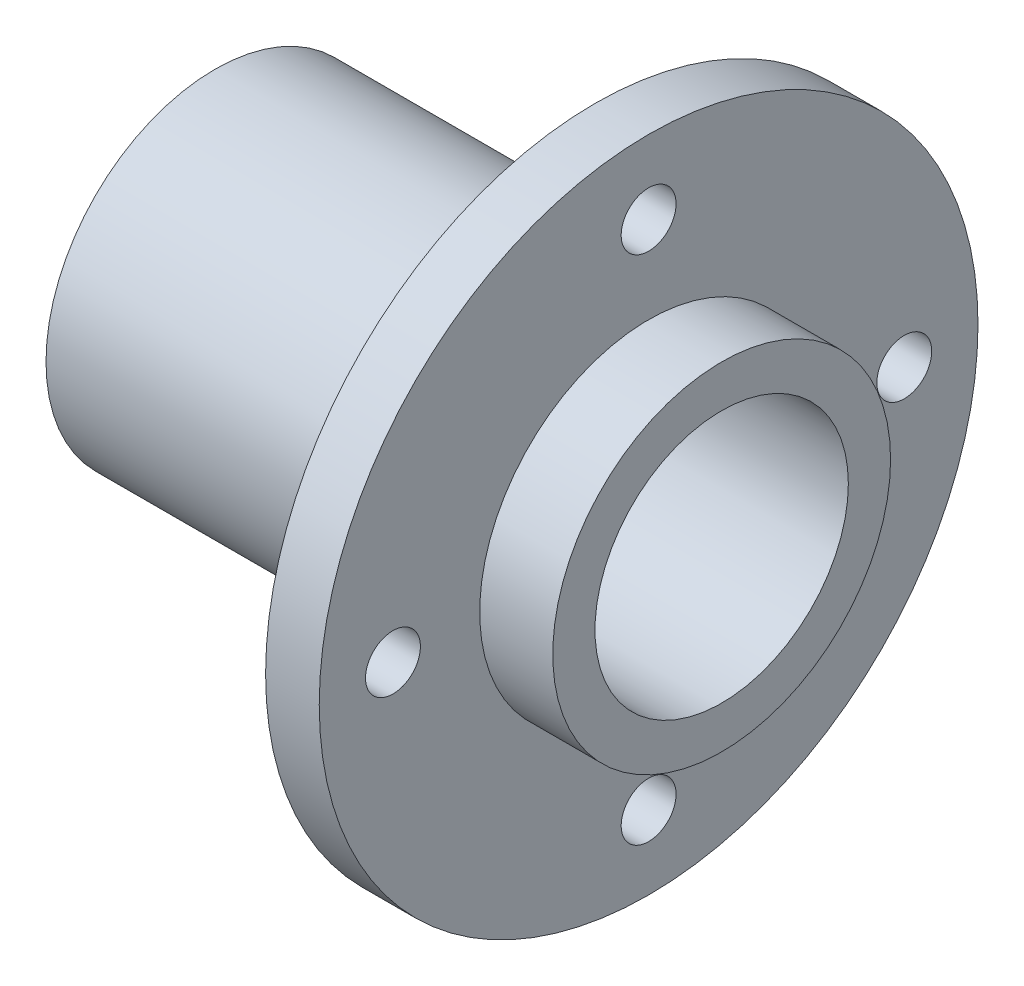
SolidWorks part; units mm, degrees
ref_plane "Front Plane" through (0, 0, 0) normal (0, 0, 1) x (1, 0, 0)
ref_plane "Top Plane" through (0, 0, 0) normal (0, 1, 0) x (1, 0, 0)
ref_plane "Right Plane" through (0, 0, 0) normal (1, 0, 0) x (0, 0, -1)
sketch "Sketch1" plane through (0, 0, 0) normal (1, 0, 0) x (0, 0, -1)
  circle A0 centre (0, 0) radius 39
  dimension "D1" = 78
extrude "Boss-Extrude1" add sketch "Sketch1" along normal blind 6.35
sketch "Sketch2" plane through (6.35, 0, 0) normal (1, 0, 0) x (0, 0, -1)
  circle A0 centre (0, 0) radius 15
  dimension "D1" = 30
extrude "Cut-Extrude1" cut sketch "Sketch2" against normal blind 6.35
sketch "Sketch3" plane through (6.35, 0, 0) normal (1, 0, 0) x (0, 0, -1)
  circle A0 centre (0, 0) radius 20
  circle A1 centre (0, 0) radius 15
  dimension "D1" = 30
  dimension "D2" = 40
extrude "Boss-Extrude2" add sketch "Sketch3" along normal blind 8.65
sketch "Sketch4" plane through (0, 0, 0) normal (-1, 0, 0) x (0, 0, 1)
  circle A0 centre (0, 0) radius 20
  circle A1 centre (0, 0) radius 15
  dimension "D1" = 40
  dimension "D2" = 30
extrude "Boss-Extrude3" add sketch "Sketch4" along normal blind 45
sketch "Sketch5" plane through (0, 0, 0) normal (-1, 0, 0) x (0, 0, 1)
  circle A0 centre (0, 30.27) radius 3.25
  circle A1 centre (-30.27, 0) radius 3.25
  circle A2 centre (30.27, 0) radius 3.25
  circle A3 centre (0, -30.27) radius 3.25
  point P9 (0, 0)
  point P10 (0, 0)
  dimension "D2" = 6.5
  dimension "D1" = 30.27
  dimension "D3" = 30.27
  dimension "D4" = 30.27
  dimension "D5" = 30.27
extrude "Cut-Extrude2" cut sketch "Sketch5" against normal blind 45
